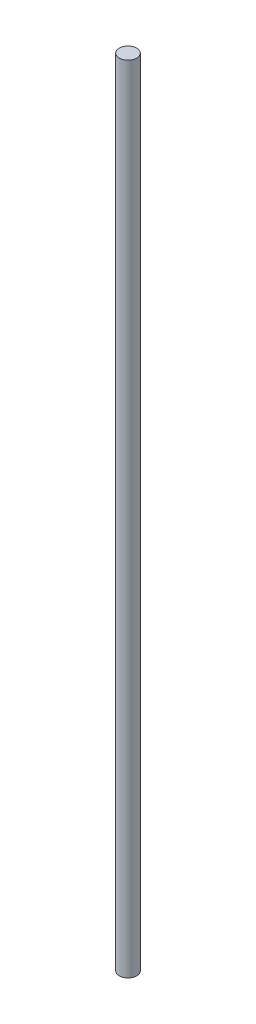
SolidWorks part; units mm, degrees
material "Plain Carbon Steel"
ref_plane "Front Plane" through (0, 0, 0) normal (0, 0, 1) x (1, 0, 0)
ref_plane "Top Plane" through (0, 0, 0) normal (0, 1, 0) x (1, 0, 0)
ref_plane "Right Plane" through (0, 0, 0) normal (1, 0, 0) x (0, 0, -1)
sketch "Sketch1" plane through (0, 0, 0) normal (0, 1, 0) x (1, 0, 0)
  circle A0 centre (0, 0) radius 2.5
  dimension "D1" = 5
extrude "Boss-Extrude1" add sketch "Sketch1" along normal blind 228.08
